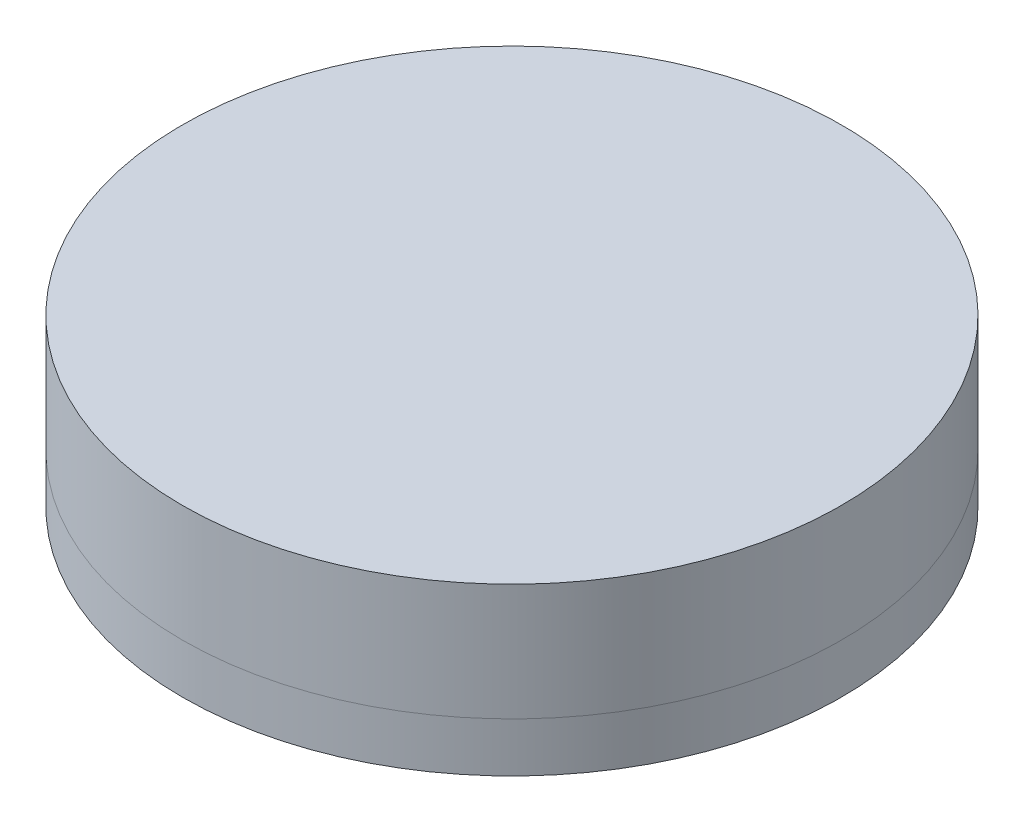
SolidWorks part; units mm, degrees
ref_plane "Front Plane" through (0, 0, 0) normal (0, 0, 1) x (1, 0, 0)
ref_plane "Top Plane" through (0, 0, 0) normal (0, 1, 0) x (1, 0, 0)
ref_plane "Right Plane" through (0, 0, 0) normal (1, 0, 0) x (0, 0, -1)
sketch "Sketch1" plane through (0, 0, 0) normal (0, 1, 0) x (1, 0, 0)
  line L5 (-12.1398, -5) -> (12.1398, 5) construction
  line L6 (-12.1398, 5) -> (12.1398, -5) construction
  circle A2 centre (0, 0) radius 10
  dimension "D1" = 20
  dimension "D2" = 10
extrude "Boss-Extrude1" add sketch "Sketch1" along normal blind 3.54
ref_axis "Axis1" through (0, 3.3141, 0) along (0, -1, 0)
sketch "Sketch2" plane through (0, 0, 0) normal (0, 0, 1) x (1, 0, 0)
  line L0 (11, 0) -> (-11, 0) construction
  line L1 (10, 0) -> (10, -1.5)
  line L2 (0.5294, 0) -> (0.5294, -0.0212)
  line L3 (10, 0) -> (0.5294, 0)
  line L4 (10, 0) -> (0.5294, 0)
  line L5 (10, 0) -> (0.5294, 0)
  line L6 (10, 0.6974) -> (10, 1.5273) construction
  line L9 (5.1783, -1.5) -> (10, -1.5)
  arc A0 (5.1783, -1.5) -> (0.5294, -0.0212) centre (-0.125, -10.125) ccw
  dimension "D1" = 20.25
  dimension "D2" = 1.5
revolve "Revolve17" add sketch "Sketch2" angle 360 about axis through (0, 3.3141, 0) along (0, -1, 0)
